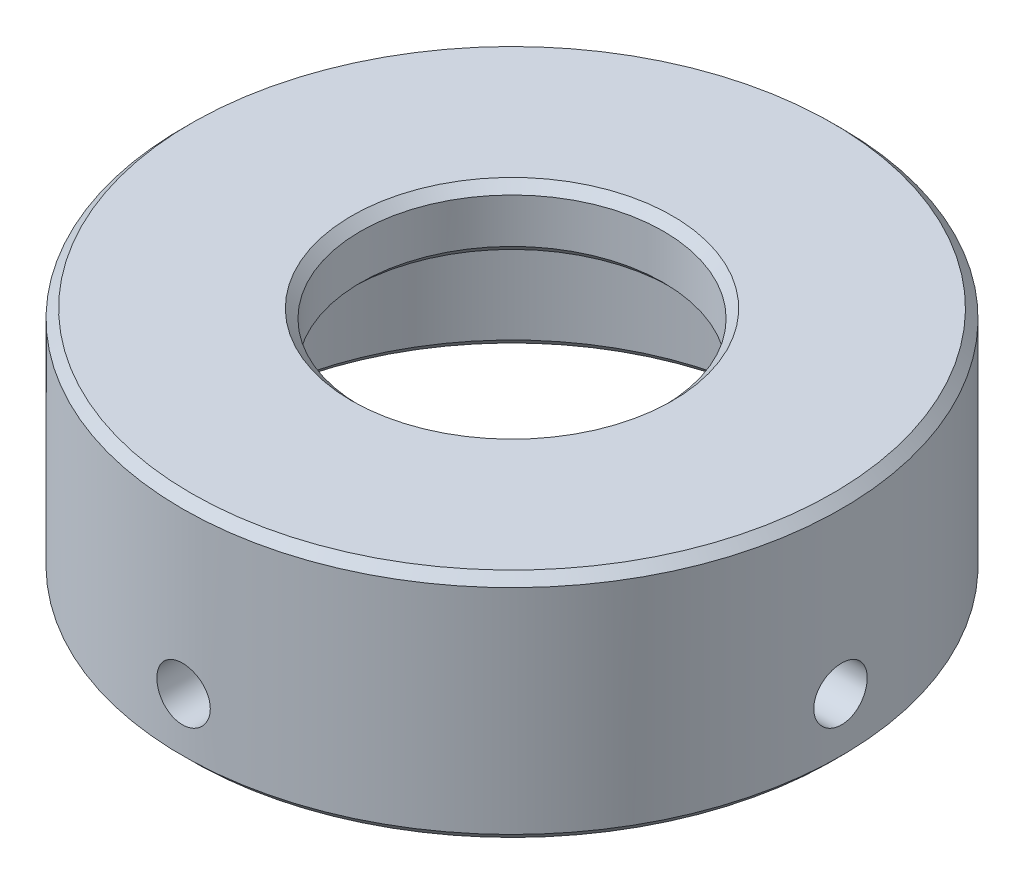
SolidWorks part; units mm, degrees
material "AISI 1020"
ref_plane "Front Plane" through (0, 0, 0) normal (0, 0, 1) x (1, 0, 0)
ref_plane "Top Plane" through (0, 0, 0) normal (0, 1, 0) x (1, 0, 0)
ref_plane "Right Plane" through (0, 0, 0) normal (1, 0, 0) x (0, 0, -1)
sketch "Sketch2" plane through (0, 0, 0) normal (0, 0, 1) x (1, 0, 0)
  line L0 (0, 0) -> (0, 31.4556) construction
  line L1 (15.5, 0) -> (15.5, -9.5)
  line L2 (8.5, 0) -> (15.5, 0)
  line L3 (8.5, 0) -> (8.5, 3.5)
  line L4 (8.5, 3.5) -> (18.5, 3.5)
  line L5 (15.5, -9.5) -> (18.5, -9.5)
  line L6 (18.5, -9.5) -> (18.5, 3.5)
  dimension "D1" = 3.5
  dimension "D2" = 3
  dimension "D3" = 8.5
  dimension "D5" = 15.5
  dimension "D8" = 9.5
revolve "Revolve1" add sketch "Sketch2" angle 360 about L0
chamfer "Chamfer1" distance 0.5 angle 45 6 edges at (0, -9.5, -18.5) (0, 3.5, -8.5) (0, 0, -8.5) (0, 0, -15.5) (0, 3.5, -18.5) (0, -9.5, -15.5)
hole_wizard "Ø3.0 (3) Diameter Hole1" positions "3DSketch1" profile "Sketch3" hole size "Ø3.0" standard "DIN"
sketch3d "3DSketch1"
  line L0 (0, 0, 0) -> (-18.5, 0, 0) construction
  line L2 (0, 0, 0) -> (0, 0, 18.5) construction
  point P0 (-18.5, -6, 0)
  point P2 (0, -6, 18.5)
  point P16 (18.5, -6, 0)
  dimension "D1" = 3.5
  dimension "D2" = 3.5
sketch "Sketch3" plane through (-18.5, -6, 0) normal (0, 1, 0) x (0, 0, 1)
  line L0 (0, 0) -> (0, 12.9013)
  line L1 (0, 12.9013) -> (1.5, 12)
  line L2 (1.5, 12) -> (1.5, 0)
  line L5 (1.5, 0) -> (0, 0)
  line L10 (0, 12.9013) -> (-1.5, 12) construction
  line L11 (0, -6.35) -> (0, 107.95) construction
  dimension "Hole Dia." = 3
  dimension "Hole Depth" = 12
  dimension "Drill Angle" = 118
